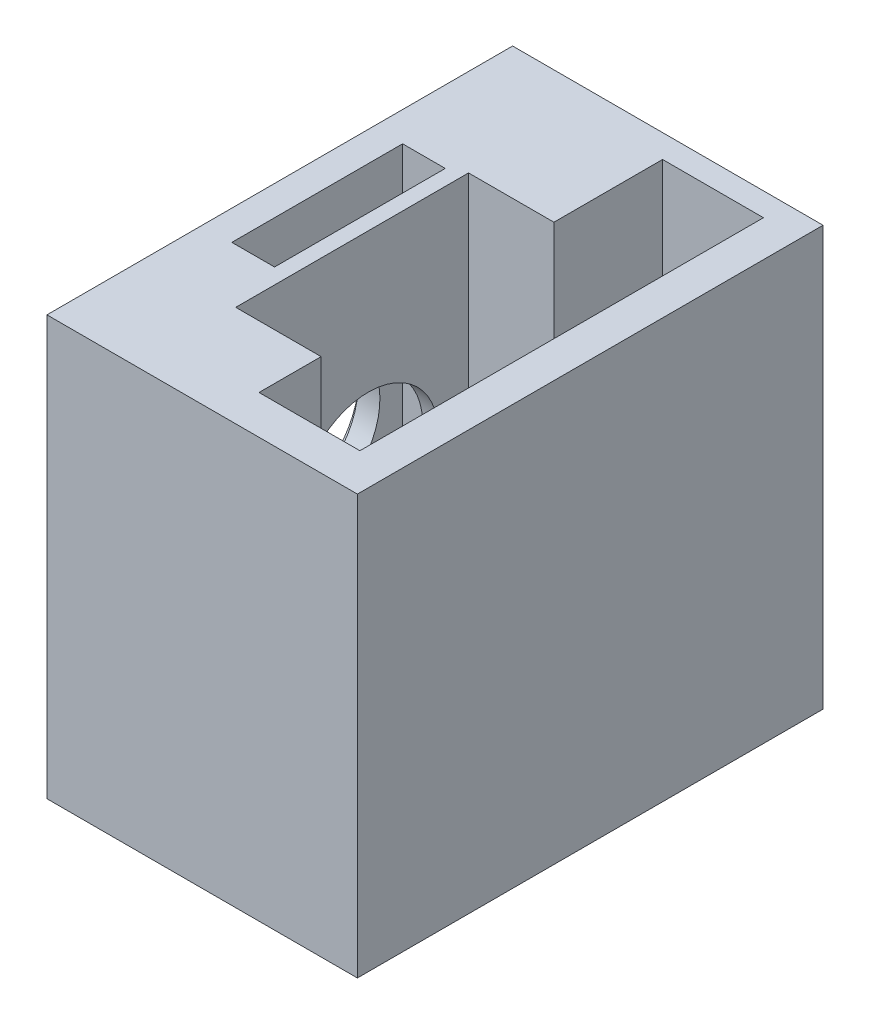
SolidWorks part; units mm, degrees
ref_plane "Front Plane" through (0, 0, 0) normal (0, 0, 1) x (1, 0, 0)
ref_plane "Top Plane" through (0, 0, 0) normal (0, 1, 0) x (1, 0, 0)
ref_plane "Right Plane" through (0, 0, 0) normal (1, 0, 0) x (0, 0, -1)
sketch "Sketch2" plane through (0, 0, 0) normal (1, 0, 0) x (0, 0, -1)
  line L1 (0, 0) -> (30, 0)
  line L2 (0, 0) -> (0, 27)
  line L3 (0, 27) -> (30, 27)
  line L4 (30, 0) -> (30, 27)
  dimension "D1" = 30
  dimension "D2" = 27
extrude "Boss-Extrude1" add sketch "Sketch2" along normal blind 20
sketch "Sketch6" plane through (2.2961, 27, -0.2935) normal (0, 1, 0) x (1, 0, 0)
  line L0 (17.7039, 29.7065) -> (-2.2961, 29.7065) construction
  line L5 (8.8658, 28.2065) -> (15.3658, 28.2065)
  line L6 (8.8658, 28.2065) -> (8.8658, 2.2065)
  line L7 (8.8658, 2.2065) -> (15.3658, 2.2065)
  line L8 (15.3658, 28.2065) -> (15.3658, 2.2065)
  dimension "D1" = 6.5
  dimension "D2" = 26
  dimension "D3" = 1.5
extrude "Cut-Extrude4" cut sketch "Sketch6" against normal blind 26 contours L8 L7 L6 L5
sketch "Sketch9" plane through (0, 27, 0) normal (0, 1, 0) x (1, 0, 0)
  line L0 (11.162, 28.5) -> (11.162, 2.5) construction
  line L1 (5.662, 21.5) -> (11.162, 21.5)
  line L2 (5.662, 21.5) -> (5.662, 6.5)
  line L3 (5.662, 6.5) -> (11.162, 6.5)
  line L4 (11.162, 21.5) -> (11.162, 6.5)
  line L5 (11.162, 28.5) -> (17.662, 28.5) construction
  line L6 (11.162, 2.5) -> (17.662, 2.5) construction
  dimension "D1" = 7
  dimension "D2" = 4
  dimension "D3" = 5.5
extrude "Cut-Extrude5" cut sketch "Sketch9" against normal blind 21
sketch "Sketch11" plane through (0, 0, 0) normal (-1, 0, 0) x (0, 0, 1)
  line L0 (-30, 27) -> (0, 27) construction
  line L1 (-30, 0) -> (-30, 27) construction
  circle A0 centre (-15.1, 13.5) radius 5
  dimension "D1" = 13.5
  dimension "D2" = 14.9
extrude "Cut-Extrude8" cut sketch "Sketch11" against normal blind 0.5
sketch "Sketch12" plane through (0, 27, 0) normal (0, 1, 0) x (1, 0, 0)
  line L0 (5.662, 21.5) -> (5.662, 6.5) construction
  line L1 (1.912, 21) -> (4.662, 21)
  line L2 (1.912, 21) -> (1.912, 10)
  line L3 (1.912, 10) -> (4.662, 10)
  line L4 (4.662, 21) -> (4.662, 10)
  line L6 (11.162, 28.5) -> (17.662, 28.5) construction
  line L7 (11.162, 2.5) -> (17.662, 2.5) construction
  point P6 (3.287, 10)
  point P9 (4.662, 15.5)
  dimension "D1" = 7.5
  dimension "D2" = 7.5
  dimension "D3" = 2.75
  dimension "D4" = 1
extrude "Cut-Extrude12" cut sketch "Sketch12" against normal blind 17.5
sketch "Sketch15" plane through (0.5, 0, 0) normal (-1, 0, 0) x (0, 0, 1)
  line L0 (-30, 0) -> (-30, 27) construction
  line L1 (-30, 27) -> (0, 27) construction
  circle A0 centre (-15.04, 13.5) radius 4.5
  dimension "D1" = 14.96
  dimension "D2" = 13.5
extrude "Cut-Extrude13" cut sketch "Sketch15" against normal blind 6
sketch "Sketch16" plane through (0, 0, 0) normal (0, 0, 1) x (1, 0, 0)
